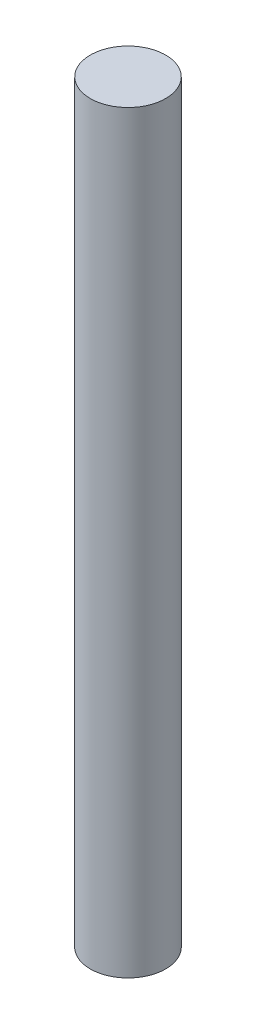
SolidWorks part; units mm, degrees
ref_plane "Front Plane" through (0, 0, 0) normal (0, 0, 1) x (1, 0, 0)
ref_plane "Top Plane" through (0, 0, 0) normal (0, 1, 0) x (1, 0, 0)
ref_plane "Right Plane" through (0, 0, 0) normal (1, 0, 0) x (0, 0, -1)
sketch "Sketch1" plane through (0, 0, 0) normal (0, 1, 0) x (1, 0, 0)
  circle A0 centre (0, 0) radius 1.5
  dimension "D1" = 3
extrude "Boss-Extrude1" add sketch "Sketch1" along normal mid plane 30
